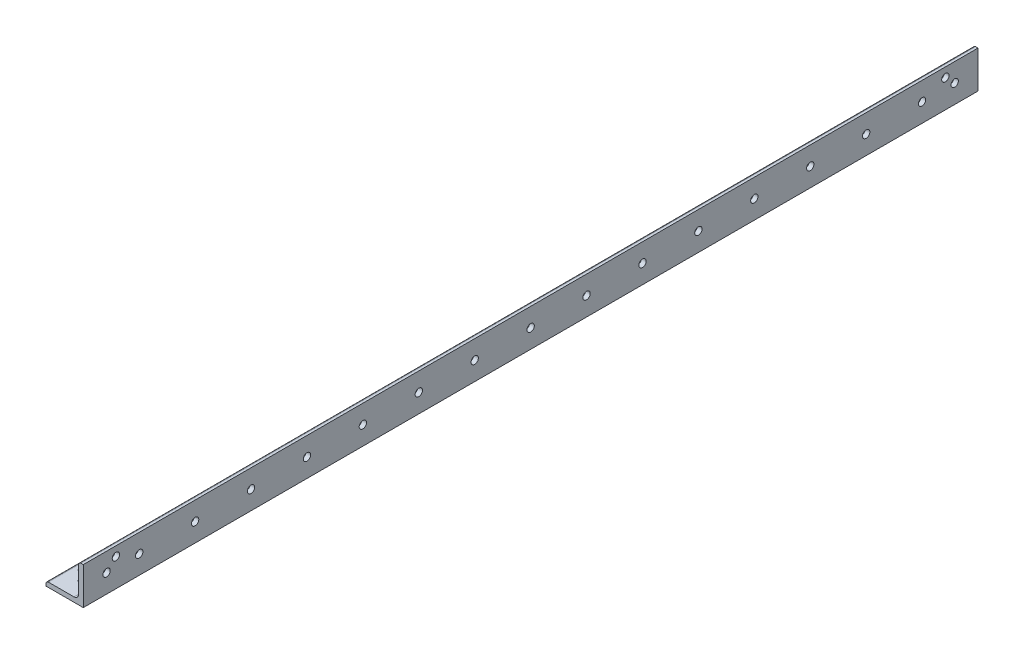
SolidWorks part; units mm, degrees
ref_plane "Front Plane" through (0, 0, 0) normal (0, 0, 1) x (1, 0, 0)
ref_plane "Top Plane" through (0, 0, 0) normal (0, 1, 0) x (1, 0, 0)
ref_plane "Right Plane" through (0, 0, 0) normal (1, 0, 0) x (0, 0, -1)
sketch "Sketch0" plane through (0, 0, 0) normal (0, 0, 1) x (1, 0, 0)
  line L0 (-12.7, -12.7) -> (12.7, -12.7)
  line L1 (12.7, -12.7) -> (12.7, 12.7)
  line L2 (12.7, 0) -> (0, 0) construction
  line L3 (0, 0) -> (0, -12.7) construction
  line L4 (9.525, -6.35) -> (9.525, 12.7) construction
  line L5 (6.35, -9.525) -> (-12.7, -9.525) construction
  arc A0 (9.525, -6.35) -> (6.35, -9.525) centre (6.35, -6.35) cw
  point P3 (8.5951, -8.5951)
  dimension "Inside Corner Radius" = 3.175
  dimension "Outside Height" = 25.4
  dimension "Inside Height" = 22.225
  dimension "Inside Width" = 22.225
  dimension "Wall Thickness" = 3.175
  dimension "D1" = 3.175
  dimension "Outside Width" = 25.4
sketch "Sketch1" plane through (0, 0, 0) normal (1, 0, 0) x (0, 0, -1)
  line L0 (304.8, 0) -> (-304.8, 0)
  point P4 (0, 0)
  dimension "Length" = 609.6
sketch "Sketch2" plane through (0, 0, 0) normal (0, 0, 1) x (1, 0, 0)
  line L0 (-12.7, -12.7) -> (12.7, -12.7)
  line L1 (12.7, -12.7) -> (12.7, 12.7)
  line L2 (12.7, 12.7) -> (9.525, 12.7) construction
  line L3 (9.525, 11.1125) -> (9.525, -6.35)
  line L4 (6.35, -9.525) -> (-11.1125, -9.525)
  line L5 (-12.7, -12.7) -> (-12.7, -9.525) construction
  line L6 (11.1125, 12.7) -> (12.7, 12.7)
  line L7 (-12.7, -11.1125) -> (-12.7, -12.7)
  line L8 (12.7, 0) -> (0, 0) construction
  line L9 (0, 0) -> (0, -12.7) construction
  arc A0 (9.525, 11.1125) -> (11.1125, 12.7) centre (11.1125, 11.1125) cw
  arc A1 (-12.7, -11.1125) -> (-11.1125, -9.525) centre (-11.1125, -11.1125) cw
  arc A2 (9.525, -6.35) -> (6.35, -9.525) centre (6.35, -6.35) cw
  dimension "Inside Radius" = 3.175
  dimension "Height" = 25.4
  dimension "Width" = 25.4
  dimension "Thickness" = 3.175
extrude "Boss-Extrude1" add sketch "Sketch2" along normal mid plane 609.6
sketch "Break Locations" plane through (0, 0, 0) normal (1, 0, 0) x (0, 0, -1)
  line L0 (-278.892, 0) -> (278.892, 0)
  line L1 (-304.8, -12.7) -> (-304.8, 12.7) construction
  line L2 (304.8, -12.7) -> (304.8, 12.7) construction
  point P0 (-283.21, 0)
  point P1 (283.21, 0)
  point P10 (0, 0)
  point P11 (278.892, 0)
  point P13 (-278.892, 0)
  dimension "D1" = 21.59
  dimension "D2" = 21.59
  dimension "D3" = 25.908
sketch "Sketch3" plane through (0, 0, 0) normal (0, 1, 0) x (1, 0, 0)
  line L0 (12.7, -304.8) -> (12.7, 304.8) construction
  line L1 (-12.7, 304.8) -> (12.7, 304.8) construction
  line L2 (12.7, -304.8) -> (12.7, 304.8) construction
  line L3 (6.35, 304.8) -> (-11.1125, 304.8) construction
  line L4 (-11.1125, 0) -> (6.35, 0) construction
  line L5 (-11.1125, -304.8) -> (-11.1125, 304.8) construction
  line L6 (6.35, -304.8) -> (6.35, 304.8) construction
  line L7 (0, 266.7) -> (0, 228.6) construction
  circle A0 centre (-6.35, 285.75) radius 2.5
  circle A1 centre (0, 292.1) radius 2.5
  circle A2 centre (0, 266.7) radius 2.5
  circle A3 centre (0, 228.6) radius 2.5
  circle A4 centre (0, 190.5) radius 2.5
  circle A5 centre (0, 152.4) radius 2.5
  circle A6 centre (0, 114.3) radius 2.5
  circle A7 centre (0, 76.2) radius 2.5
  circle A8 centre (0, 38.1) radius 2.5
  circle A9 centre (0, 0) radius 2.5
  circle A10 centre (0, -38.1) radius 2.5
  circle A11 centre (0, -76.2) radius 2.5
  circle A12 centre (0, -114.3) radius 2.5
  circle A13 centre (0, -292.1) radius 2.5
  circle A14 centre (-6.35, -285.75) radius 2.5
  circle A15 centre (0, -152.4) radius 2.5
  circle A16 centre (0, -190.5) radius 2.5
  circle A17 centre (0, -228.6) radius 2.5
  circle A18 centre (0, -266.7) radius 2.5
  dimension "D3" = 5
  dimension "D1" = 12.7
  dimension "D2" = 12.7
  dimension "D4" = 19.05
  dimension "D5" = 19.05
  dimension "D6" = 12.7
  dimension "D7" = 38.1
  dimension "D9" = 38.1
  dimension "D8" = 15
extrude "Cut-Extrude2" cut sketch "Sketch3" against normal blind 254
sketch "Sketch8" plane through (12.7, 0, -12.7) normal (-1, 0, 0) x (0, 0, 1)
  line L0 (317.5, -6.35) -> (-292.1, -6.35) construction
  line L1 (317.5, 11.1125) -> (-292.1, 11.1125) construction
  line L2 (317.5, -12.7) -> (-292.1, -12.7) construction
  line L3 (-292.1, 11.1125) -> (-292.1, -6.35) construction
  line L4 (12.7, 11.1125) -> (12.7, -6.35) construction
  line L5 (317.5, 11.1125) -> (317.5, -6.35) construction
  line L7 (279.4, 0) -> (241.3, 0) construction
  circle A0 centre (295.275, 6.35) radius 2.5
  circle A1 centre (301.625, 0) radius 2.5
  circle A2 centre (279.4, 0) radius 2.5
  circle A3 centre (241.3, 0) radius 2.5
  circle A4 centre (203.2, 0) radius 2.5
  circle A5 centre (165.1, 0) radius 2.5
  circle A6 centre (127, 0) radius 2.5
  circle A7 centre (88.9, 0) radius 2.5
  circle A8 centre (50.8, 0) radius 2.5
  circle A9 centre (12.7, 0) radius 2.5
  circle A10 centre (-25.4, 0) radius 2.5
  circle A11 centre (-63.5, 0) radius 2.5
  circle A12 centre (-101.6, 0) radius 2.5
  circle A13 centre (-276.225, 0) radius 2.5
  circle A14 centre (-269.875, 6.35) radius 2.5
  circle A15 centre (-139.7, 0) radius 2.5
  circle A16 centre (-177.8, 0) radius 2.5
  circle A17 centre (-215.9, 0) radius 2.5
  circle A18 centre (-254, 0) radius 2.5
  dimension "D3" = 5
  dimension "D1" = 12.7
  dimension "D2" = 12.7
  dimension "D4" = 15.875
  dimension "D5" = 19.05
  dimension "D6" = 22.225
  dimension "D7" = 38.1
  dimension "D9" = 38.1
  dimension "D8" = 15
extrude "Cut-Extrude4" cut sketch "Sketch8" along normal blind 254
sketch "Sketch9" plane through (0, -12.7, 0) normal (0, 1, 0) x (0, 0, -1)
  line L0 (-16, 0) -> (0, 0) construction
  line L1 (0, 0) -> (0, -12.7) construction
  line L2 (-304.8, -12.7) -> (304.8, -12.7) construction
  circle A0 centre (-16, 0) radius 2.25
  circle A2 centre (16, 0) radius 2.25
  dimension "D2" = 4.5
  dimension "D1" = 16
extrude "Cut-Extrude5" cut sketch "Sketch9" along normal blind 25.4
equation "\"D1@Break Locations\" = .85 * \"Height@Sketch2\""
equation "\"D2@Break Locations\"=\"D1@Break Locations\""
equation "\"Thickness@Sketch2\" = \"Wall Thickness@Sketch0\""
equation "\"Height@Sketch2\" = \"Outside Height@Sketch0\""
equation "\"Width@Sketch2\" = \"Outside Width@Sketch0\""
equation "\"Inside Radius@Sketch2\" = \"Inside Corner Radius@Sketch0\""
equation "\"Length@Boss-Extrude1\" = \"Length@Sketch1\""
equation "\"D3@Break Locations\"=\"D2@Break Locations\"*1.2"
equation "\"D1@Sketch0\"=\"Wall Thickness@Sketch0\""
